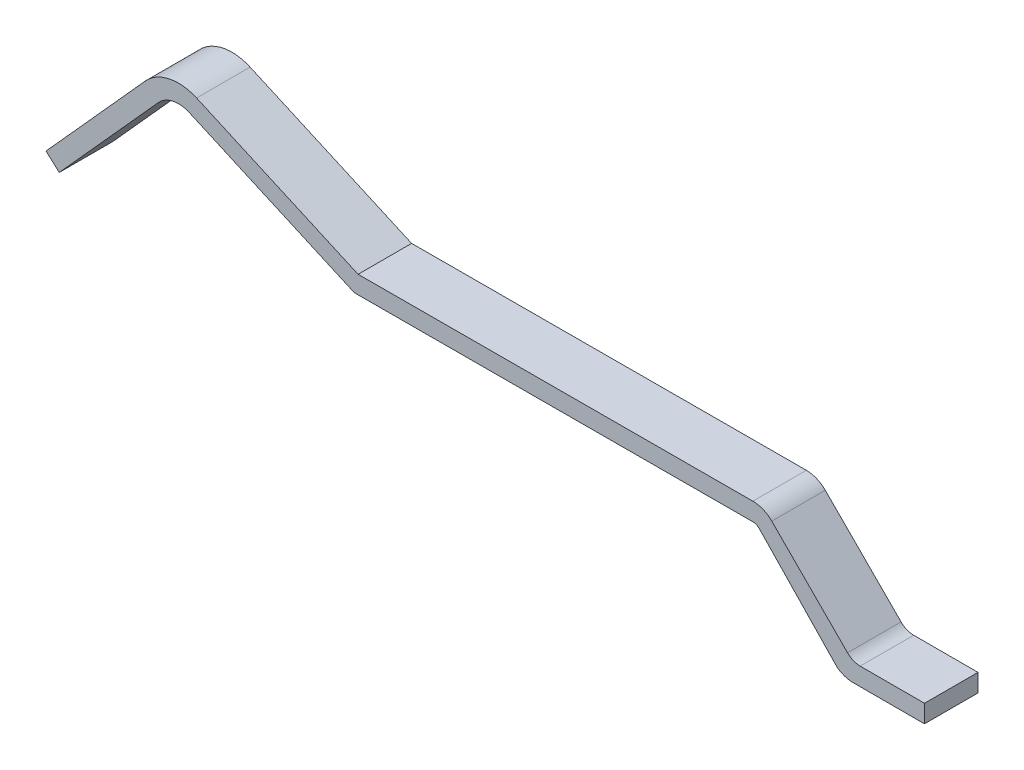
SolidWorks part; units mm, degrees
ref_plane "Plano frontal" through (0, 0, 0) normal (0, 0, 1) x (1, 0, 0)
ref_plane "Plano superior" through (0, 0, 0) normal (0, 1, 0) x (1, 0, 0)
ref_plane "Plano direito" through (0, 0, 0) normal (1, 0, 0) x (0, 0, -1)
sketch "Esboço1" plane through (0, 0, 0) normal (0, 0, 1) x (1, 0, 0)
  line L0 (18.8, 0.2) -> (18.8, 0)
  line L1 (18.8, 0) -> (18, 0)
  line L3 (17.82, 0.06) -> (16.9464, 0.9707)
  line L5 (16.8757, 1) -> (12.4075, 0.99)
  line L8 (12.4075, 0.99) -> (10.558, 1.8135)
  line L11 (10.213, 1.7401) -> (9.0995, 0.5035)
  line L12 (9.0995, 0.5035) -> (8.9509, 0.6373)
  line L13 (8.9509, 0.6373) -> (10.0644, 1.874)
  line L17 (10.6393, 1.9962) -> (12.45, 1.19)
  line L19 (12.45, 1.19) -> (16.8757, 1.2)
  line L21 (17.0879, 1.1121) -> (17.9373, 0.2589)
  line L22 (18.079, 0.2) -> (18.8, 0.2)
  arc A2 (17.9373, 0.2589) -> (18.079, 0.2) centre (18.079, 0.4) ccw
  arc A3 (18, 0) -> (17.82, 0.06) centre (18, 0.3) cw
  arc A4 (16.8757, 1) -> (16.9464, 0.9707) centre (16.876, 0.9005) cw
  arc A5 (17.0879, 1.1121) -> (16.8757, 1.2) centre (16.8764, 0.9016) ccw
  arc A6 (10.558, 1.8135) -> (10.213, 1.7401) centre (10.436, 1.5394) ccw
  arc A7 (10.6393, 1.9962) -> (10.0644, 1.874) centre (10.436, 1.5394) ccw
  dimension "D1" = 0.2
extrude "Ressalto-extrusão1" add sketch "Esboço1" along normal mid plane 0.6
